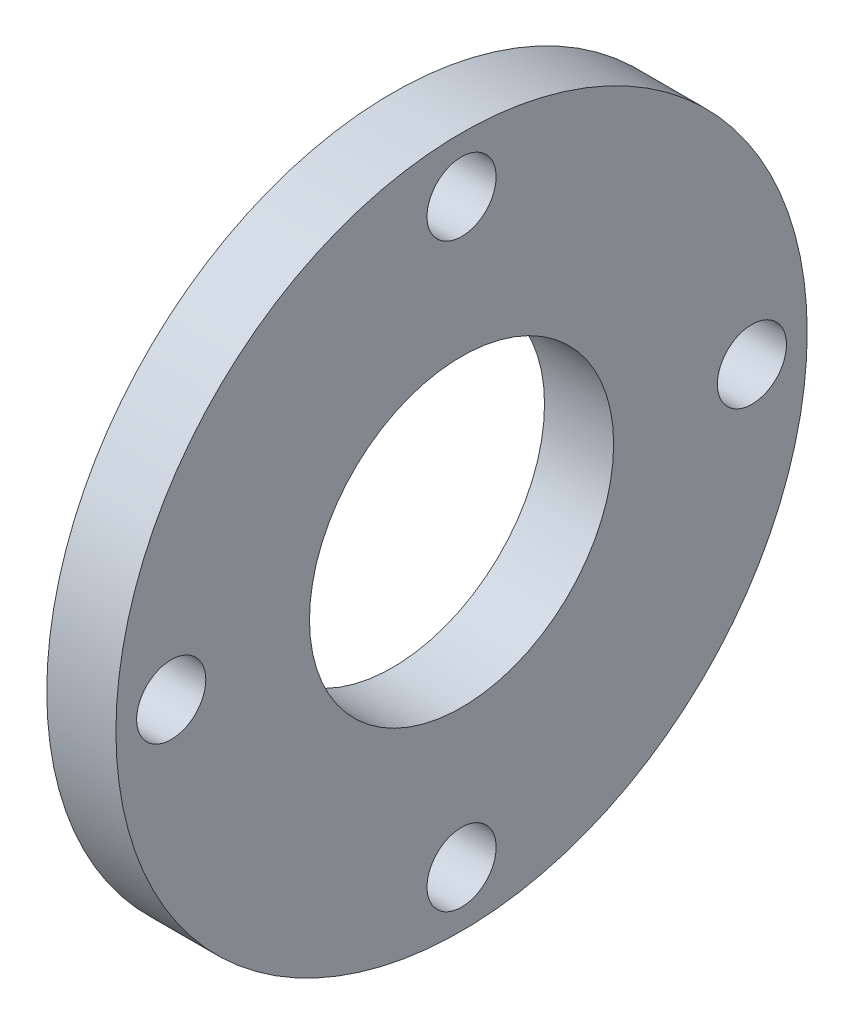
SolidWorks part; units mm, degrees
ref_plane "Alzado" through (0, 0, 0) normal (0, 0, 1) x (1, 0, 0)
ref_plane "Planta" through (0, 0, 0) normal (0, 1, 0) x (1, 0, 0)
ref_plane "Vista lateral" through (0, 0, 0) normal (1, 0, 0) x (0, 0, -1)
sketch "Croquis1" plane through (0, 0, 0) normal (1, 0, 0) x (0, 0, -1)
  circle A0 centre (0, 0) radius 25
  circle A1 centre (0, 0) radius 11
  dimension "D1" = 22
  dimension "D2" = 50
extrude "Saliente-Extruir1" add sketch "Croquis1" along normal blind 5
sketch "Croquis2" plane through (5, 0, 0) normal (1, 0, 0) x (0, 0, -1)
  circle A0 centre (0, 0) radius 21 construction
  circle A1 centre (0, 21) radius 2.5
  circle A2 centre (21, 0) radius 2.5
  circle A3 centre (0, -21) radius 2.5
  circle A4 centre (-21, 0) radius 2.5
  point P14 (0, 0)
  dimension "D1" = 42
  dimension "D3" = 5
  dimension "D2" = 4
extrude "Cortar-Extruir1" cut sketch "Croquis2" against normal blind 10
sketch "Croquis3" plane through (5, 0, 0) normal (1, 0, 0) x (0, 0, -1)
  circle A0 centre (0, -21) radius 2.5 construction
  circle A1 centre (0, 0) radius 25
  circle A2 centre (0, 0) radius 25
  circle A3 centre (21, 0) radius 2.5 construction
  circle A4 centre (0, 21) radius 2.5 construction
  circle A5 centre (-21, 0) radius 2.5 construction
  circle A6 centre (0, 0) radius 11 construction
  circle A7 centre (0, -21) radius 2.5
  circle A8 centre (21, 0) radius 2.5
  circle A9 centre (0, 21) radius 2.5
  circle A10 centre (-21, 0) radius 2.5
  circle A11 centre (0, 0) radius 11
  dimension "D1" = 0
